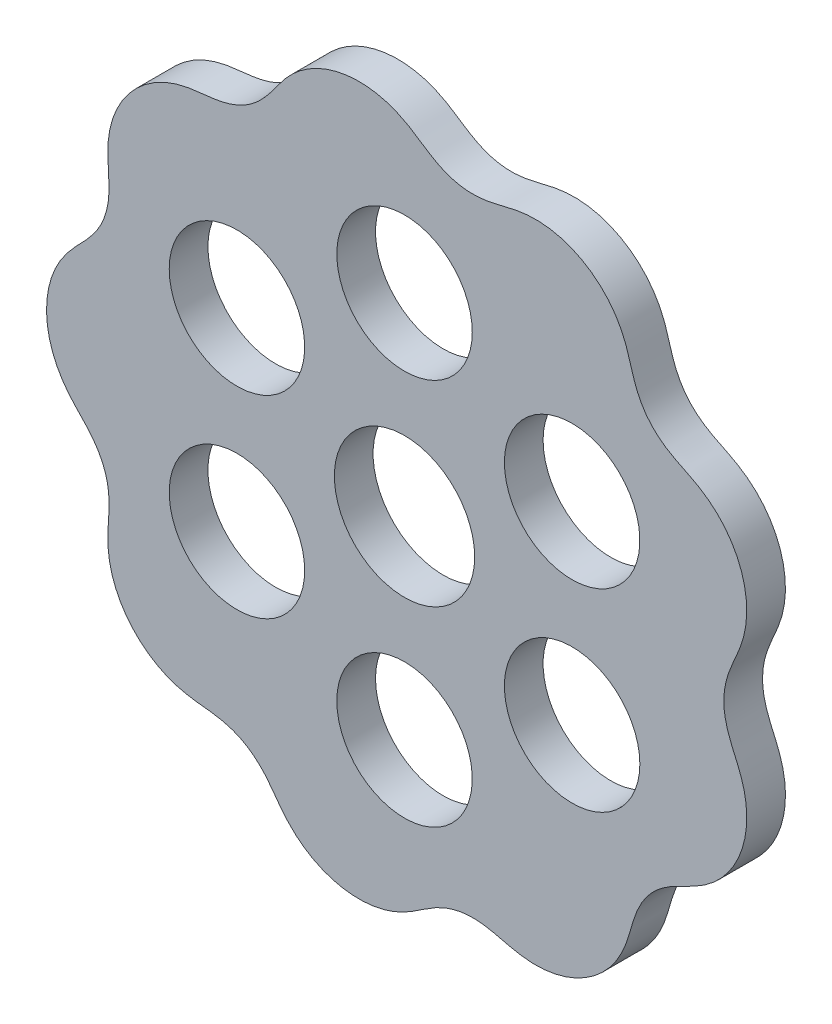
SolidWorks part; units mm, degrees
ref_plane "Front Plane" through (0, 0, 0) normal (0, 0, 1) x (1, 0, 0)
ref_plane "Top Plane" through (0, 0, 0) normal (0, 1, 0) x (1, 0, 0)
ref_plane "Right Plane" through (0, 0, 0) normal (1, 0, 0) x (0, 0, -1)
curve "Curve2"
  spline degree 3 poles (33.0063, -0.3751, 0) (32.9968, 0, 0) (33.0063, 0.3751, 0) (33.034, 0.7448, 0) (33.0785, 1.1045, 0) (33.1373, 1.45, 0) (33.2077, 1.7787, 0) (33.2869, 2.0891, 0) (33.3721, 2.3805, 0) (33.4609, 2.6535, 0) (33.5515, 2.909, 0) (33.6424, 3.1486, 0) (33.7324, 3.3741, 0) (33.821, 3.5871, 0) (33.9077, 3.7897, 0) (33.9923, 3.9834, 0) (34.0747, 4.17, 0) (34.1549, 4.3509, 0) (34.2329, 4.5275, 0) (34.3089, 4.701, 0) (34.383, 4.8725, 0) (34.4551, 5.0429, 0) (34.5253, 5.2131, 0) (34.5937, 5.3838, 0) (34.6602, 5.5556, 0) (34.7247, 5.7292, 0) (34.7873, 5.9049, 0) (34.8477, 6.0832, 0) (34.9059, 6.2645, 0) (34.9616, 6.4489, 0) (35.0148, 6.6368, 0) (35.0651, 6.8282, 0) (35.1125, 7.0234, 0) (35.1566, 7.2223, 0) (35.1972, 7.4251, 0) (35.2342, 7.6317, 0) (35.2672, 7.8421, 0) (35.2961, 8.0561, 0) (35.3206, 8.2737, 0) (35.3404, 8.4948, 0) (35.3554, 8.7191, 0) (35.3653, 8.9466, 0) (35.3699, 9.1768, 0) (35.3692, 9.4097, 0) (35.3628, 9.6449, 0) (35.3506, 9.8822, 0) (35.3325, 10.1213, 0) (35.3084, 10.3618, 0) (35.2782, 10.6035, 0) (35.2418, 10.846, 0) (35.1992, 11.0889, 0) (35.1503, 11.332, 0) (35.0951, 11.5748, 0) (35.0336, 11.817, 0) (34.9658, 12.0583, 0) (34.8919, 12.2983, 0) (34.8119, 12.5367, 0) (34.7259, 12.773, 0) (34.634, 13.007, 0) (34.5363, 13.2384, 0) (34.4331, 13.4668, 0) (34.3245, 13.6919, 0) (34.2107, 13.9134, 0) (34.0919, 14.131, 0) (33.9685, 14.3445, 0) (33.8405, 14.5537, 0) (33.7083, 14.7582, 0) (33.5721, 14.958, 0) (33.4323, 15.1527, 0) (33.2891, 15.3423, 0) (33.1428, 15.5266, 0) (32.9937, 15.7055, 0) (32.8421, 15.8789, 0) (32.6883, 16.0467, 0) (32.5327, 16.209, 0) (32.3754, 16.3656, 0) (32.2168, 16.5165, 0) (32.0571, 16.662, 0) (31.8965, 16.8019, 0) (31.7354, 16.9364, 0) (31.5739, 17.0656, 0) (31.4123, 17.1896, 0) (31.2505, 17.3087, 0) (31.0889, 17.423, 0) (30.9274, 17.5327, 0) (30.7662, 17.6382, 0) (30.6051, 17.7396, 0) (30.4442, 17.8374, 0) (30.2833, 17.9318, 0) (30.1223, 18.0233, 0) (29.9609, 18.1122, 0) (29.7988, 18.199, 0) (29.6356, 18.2842, 0) (29.4709, 18.3684, 0) (29.3039, 18.4522, 0) (29.1342, 18.5362, 0) (28.9609, 18.6213, 0) (28.7832, 18.7084, 0) (28.6001, 18.7984, 0) (28.4108, 18.8924, 0) (28.2142, 18.9918, 0) (28.0094, 19.0981, 0) (27.7954, 19.2129, 0) (27.5718, 19.3381, 0) (27.3382, 19.4756, 0) (27.0947, 19.6276, 0) (26.8421, 19.7961, 0) (26.582, 19.9829, 0) (26.3167, 20.1895, 0) (26.0495, 20.4164, 0) (25.7843, 20.6633, 0) (25.5254, 20.9287, 0) (25.2771, 21.21, 0) (25.0432, 21.5034, 0) (24.8267, 21.8044, 0) (24.6296, 22.1085, 0) (24.4526, 22.411, 0) (24.2953, 22.7081, 0) (24.1564, 22.9967, 0) (24.0344, 23.2747, 0) (23.927, 23.541, 0) (23.8321, 23.7949, 0) (23.7476, 24.0369, 0) (23.6717, 24.2675, 0) (23.6026, 24.4877, 0) (23.5389, 24.6985, 0) (23.4791, 24.9013, 0) (23.4223, 25.0972, 0) (23.3674, 25.2873, 0) (23.3137, 25.4728, 0) (23.2604, 25.6546, 0) (23.2069, 25.8335, 0) (23.1526, 26.0104, 0) (23.097, 26.1859, 0) (23.0397, 26.3606, 0) (22.9801, 26.535, 0) (22.918, 26.7094, 0) (22.853, 26.8842, 0) (22.7847, 27.0597, 0) (22.7127, 27.2359, 0) (22.6369, 27.413, 0) (22.5568, 27.5911, 0) (22.4723, 27.7701, 0) (22.3832, 27.9501, 0) (22.2891, 28.1309, 0) (22.1899, 28.3123, 0) (22.0854, 28.4943, 0) (21.9755, 28.6767, 0) (21.86, 28.8592, 0) (21.7389, 29.0417, 0) (21.6119, 29.2238, 0) (21.4792, 29.4052, 0) (21.3406, 29.5858, 0) (21.1962, 29.7652, 0) (21.0459, 29.9431, 0) (20.8898, 30.1192, 0) (20.728, 30.2931, 0) (20.5605, 30.4647, 0) (20.3874, 30.6334, 0) (20.2089, 30.7991, 0) (20.0252, 30.9615, 0) (19.8363, 31.1202, 0) (19.6426, 31.2749, 0) (19.4442, 31.4255, 0) (19.2414, 31.5715, 0) (19.0344, 31.7128, 0) (18.8236, 31.8491, 0) (18.609, 31.9803, 0) (18.3912, 32.1061, 0) (18.1704, 32.2262, 0) (17.9469, 32.3407, 0) (17.721, 32.4493, 0) (17.4931, 32.5519, 0) (17.2636, 32.6485, 0) (17.0327, 32.7389, 0) (16.8009, 32.823, 0) (16.5684, 32.901, 0) (16.3356, 32.9727, 0) (16.1029, 33.0382, 0) (15.8706, 33.0975, 0) (15.6391, 33.1507, 0) (15.4085, 33.1978, 0) (15.1793, 33.2391, 0) (14.9518, 33.2745, 0) (14.7261, 33.3042, 0) (14.5026, 33.3284, 0) (14.2814, 33.3472, 0) (14.0628, 33.3609, 0) (13.847, 33.3697, 0) (13.6341, 33.3737, 0) (13.4243, 33.3732, 0) (13.2175, 33.3683, 0) (13.0139, 33.3594, 0) (12.8135, 33.3467, 0) (12.6162, 33.3303, 0) (12.4219, 33.3106, 0) (12.2306, 33.2877, 0) (12.042, 33.2619, 0) (11.8559, 33.2334, 0) (11.672, 33.2023, 0) (11.4899, 33.1689, 0) (11.3091, 33.1332, 0) (11.1291, 33.0955, 0) (10.9493, 33.0559, 0) (10.769, 33.0145, 0) (10.5873, 32.9714, 0) (10.4032, 32.9267, 0) (10.2158, 32.8805, 0) (10.0237, 32.8329, 0) (9.8256, 32.7842, 0) (9.6201, 32.7345, 0) (9.4056, 32.6843, 0) (9.1804, 32.6341, 0) (8.9427, 32.5845, 0) (8.691, 32.5366, 0) (8.4236, 32.4918, 0) (8.1393, 32.4517, 0) (7.8375, 32.4185, 0) (7.5182, 32.3944, 0) (7.1822, 32.3821, 0) (6.8317, 32.3841, 0) (6.4698, 32.4028, 0) (6.1009, 32.4397, 0) (5.7298, 32.4956, 0) (5.3621, 32.57, 0) (5.0028, 32.6615, 0) (4.6563, 32.7677, 0) (4.3262, 32.8857, 0) (4.0147, 33.0121, 0) (3.7229, 33.144, 0) (3.4507, 33.2785, 0) (3.1973, 33.4134, 0) (2.9613, 33.5469, 0) (2.7411, 33.678, 0) (2.5348, 33.8059, 0) (2.3403, 33.9301, 0) (2.1559, 34.0507, 0) (1.9798, 34.1676, 0) (1.8104, 34.2812, 0) (1.6461, 34.3915, 0) (1.4857, 34.4991, 0) (1.3281, 34.604, 0) (1.1721, 34.7067, 0) (1.0168, 34.8073, 0) (0.8614, 34.906, 0) (0.7051, 35.003, 0) (0.5475, 35.0983, 0) (0.3878, 35.192, 0) (0.2256, 35.2841, 0) (0.0604, 35.3746, 0) (-0.1079, 35.4634, 0) (-0.2799, 35.5503, 0) (-0.4557, 35.6353, 0) (-0.6355, 35.7181, 0) (-0.8195, 35.7986, 0) (-1.0077, 35.8766, 0) (-1.2004, 35.9519, 0) (-1.3974, 36.0242, 0) (-1.5988, 36.0932, 0) (-1.8046, 36.1588, 0) (-2.0147, 36.2207, 0) (-2.229, 36.2786, 0) (-2.4473, 36.3323, 0) (-2.6695, 36.3816, 0) (-2.8955, 36.4261, 0) (-3.125, 36.4658, 0) (-3.3577, 36.5003, 0) (-3.5935, 36.5296, 0) (-3.8321, 36.5533, 0) (-4.0731, 36.5713, 0) (-4.3164, 36.5835, 0) (-4.5615, 36.5898, 0) (-4.8082, 36.59, 0) (-5.056, 36.584, 0) (-5.3047, 36.5718, 0) (-5.554, 36.5533, 0) (-5.8034, 36.5285, 0) (-6.0526, 36.4974, 0) (-6.3012, 36.46, 0) (-6.5489, 36.4163, 0) (-6.7953, 36.3664, 0) (-7.0401, 36.3104, 0) (-7.2829, 36.2485, 0) (-7.5235, 36.1806, 0) (-7.7614, 36.107, 0) (-7.9963, 36.0278, 0) (-8.228, 35.9433, 0) (-8.4562, 35.8536, 0) (-8.6806, 35.7589, 0) (-8.901, 35.6595, 0) (-9.1171, 35.5556, 0) (-9.3286, 35.4475, 0) (-9.5355, 35.3354, 0) (-9.7376, 35.2197, 0) (-9.9347, 35.1005, 0) (-10.1267, 34.9782, 0) (-10.3135, 34.8531, 0) (-10.495, 34.7254, 0) (-10.6712, 34.5954, 0) (-10.8422, 34.4634, 0) (-11.0078, 34.3296, 0) (-11.1683, 34.1943, 0) (-11.3236, 34.0577, 0) (-11.4738, 33.92, 0) (-11.6191, 33.7814, 0) (-11.7598, 33.6421, 0) (-11.8959, 33.5021, 0) (-12.0277, 33.3616, 0) (-12.1556, 33.2206, 0) (-12.2798, 33.0791, 0) (-12.4007, 32.9371, 0) (-12.5188, 32.7944, 0) (-12.6343, 32.6509, 0) (-12.748, 32.5063, 0) (-12.8602, 32.3604, 0) (-12.9718, 32.2128, 0) (-13.0833, 32.0629, 0) (-13.1955, 31.9104, 0) (-13.3094, 31.7545, 0) (-13.426, 31.5946, 0) (-13.5464, 31.4299, 0) (-13.6719, 31.2598, 0) (-13.804, 31.0834, 0) (-13.9442, 30.9002, 0) (-14.0944, 30.7095, 0) (-14.2565, 30.511, 0) (-14.4325, 30.3048, 0) (-14.6245, 30.0913, 0) (-14.8343, 29.8718, 0) (-15.0634, 29.6481, 0) (-15.3129, 29.4227, 0) (-15.5827, 29.199, 0) (-15.8719, 28.9807, 0) (-16.1783, 28.7718, 0) (-16.4984, 28.5761, 0) (-16.828, 28.3967, 0) (-17.1621, 28.2359, 0) (-17.4957, 28.0945, 0) (-17.8244, 27.9727, 0) (-18.1443, 27.8694, 0) (-18.4526, 27.7828, 0) (-18.7476, 27.7108, 0) (-19.0284, 27.6513, 0) (-19.295, 27.602, 0) (-19.548, 27.5608, 0) (-19.7882, 27.5261, 0) (-20.0171, 27.4963, 0) (-20.2358, 27.4701, 0) (-20.4459, 27.4465, 0) (-20.6487, 27.4245, 0) (-20.8455, 27.4035, 0) (-21.0374, 27.3828, 0) (-21.2257, 27.3619, 0) (-21.4112, 27.3403, 0) (-21.5948, 27.3175, 0) (-21.7773, 27.2932, 0) (-21.9593, 27.2671, 0) (-22.1414, 27.2388, 0) (-22.324, 27.2079, 0) (-22.5074, 27.1742, 0) (-22.6921, 27.1374, 0) (-22.8781, 27.0971, 0) (-23.0657, 27.0532, 0) (-23.255, 27.0053, 0) (-23.446, 26.9532, 0) (-23.6387, 26.8966, 0) (-23.833, 26.8353, 0) (-24.029, 26.7691, 0) (-24.2264, 26.6979, 0) (-24.4251, 26.6213, 0) (-24.6249, 26.5393, 0) (-24.8256, 26.4516, 0) (-25.0269, 26.3583, 0) (-25.2287, 26.2591, 0) (-25.4306, 26.154, 0) (-25.6323, 26.0429, 0) (-25.8336, 25.9257, 0) (-26.0341, 25.8026, 0) (-26.2335, 25.6734, 0) (-26.4315, 25.5382, 0) (-26.6278, 25.3971, 0) (-26.822, 25.2501, 0) (-27.0138, 25.0973, 0) (-27.2029, 24.9389, 0) (-27.3889, 24.775, 0) (-27.5716, 24.6058, 0) (-27.7506, 24.4314, 0) (-27.9257, 24.2521, 0) (-28.0966, 24.0681, 0) (-28.263, 23.8797, 0) (-28.4247, 23.687, 0) (-28.5814, 23.4904, 0) (-28.7329, 23.2901, 0) (-28.8791, 23.0866, 0) (-29.0198, 22.88, 0) (-29.1547, 22.6707, 0) (-29.2838, 22.459, 0) (-29.4069, 22.2453, 0) (-29.5241, 22.0299, 0) (-29.6351, 21.8131, 0) (-29.74, 21.5953, 0) (-29.8388, 21.3769, 0) (-29.9314, 21.158, 0) (-30.0178, 20.9392, 0) (-30.0982, 20.7206, 0) (-30.1726, 20.5027, 0) (-30.2411, 20.2856, 0) (-30.3037, 20.0696, 0) (-30.3607, 19.8551, 0) (-30.4121, 19.6423, 0) (-30.4582, 19.4312, 0) (-30.4991, 19.2223, 0) (-30.5351, 19.0155, 0) (-30.5662, 18.8111, 0) (-30.5928, 18.609, 0) (-30.615, 18.4094, 0) (-30.6332, 18.2123, 0) (-30.6475, 18.0176, 0) (-30.6582, 17.8252, 0) (-30.6655, 17.635, 0) (-30.6697, 17.4467, 0) (-30.6711, 17.2602, 0) (-30.6698, 17.075, 0) (-30.666, 16.8908, 0) (-30.6602, 16.707, 0) (-30.6524, 16.5231, 0) (-30.6429, 16.3383, 0) (-30.632, 16.1519, 0) (-30.6199, 15.9628, 0) (-30.607, 15.7702, 0) (-30.5935, 15.5728, 0) (-30.5799, 15.3693, 0) (-30.5667, 15.1583, 0) (-30.5545, 14.9383, 0) (-30.5441, 14.7078, 0) (-30.5366, 14.4651, 0) (-30.5332, 14.2089, 0) (-30.5355, 13.9378, 0) (-30.5453, 13.6509, 0) (-30.565, 13.3479, 0) (-30.5967, 13.0292, 0) (-30.6429, 12.6962, 0) (-30.7058, 12.3513, 0) (-30.7871, 11.9982, 0) (-30.8875, 11.6413, 0) (-31.0069, 11.2856, 0) (-31.144, 10.9363, 0) (-31.2966, 10.5984, 0) (-31.4613, 10.2756, 0) (-31.6348, 9.9711, 0) (-31.8134, 9.6863, 0) (-31.994, 9.4217, 0) (-32.1737, 9.177, 0) (-32.3505, 8.9509, 0) (-32.5231, 8.7417, 0) (-32.6904, 8.5476, 0) (-32.8521, 8.3666, 0) (-33.0082, 8.1967, 0) (-33.159, 8.036, 0) (-33.3047, 7.8829, 0) (-33.446, 7.7357, 0) (-33.5832, 7.5931, 0) (-33.7169, 7.4539, 0) (-33.8477, 7.3168, 0) (-33.9759, 7.181, 0) (-34.1019, 7.0455, 0) (-34.2261, 6.9096, 0) (-34.3488, 6.7726, 0) (-34.47, 6.6339, 0) (-34.59, 6.4929, 0) (-34.7089, 6.3492, 0) (-34.8267, 6.2023, 0) (-34.9433, 6.0518, 0) (-35.0588, 5.8976, 0) (-35.173, 5.7392, 0) (-35.2858, 5.5765, 0) (-35.3971, 5.4093, 0) (-35.5066, 5.2375, 0) (-35.6141, 5.0608, 0) (-35.7195, 4.8794, 0) (-35.8225, 4.693, 0) (-35.9228, 4.5017, 0) (-36.0203, 4.3056, 0) (-36.1145, 4.1046, 0) (-36.2053, 3.8989, 0) (-36.2924, 3.6886, 0) (-36.3755, 3.4738, 0) (-36.4544, 3.2547, 0) (-36.5289, 3.0315, 0) (-36.5986, 2.8044, 0) (-36.6634, 2.5735, 0) (-36.723, 2.3393, 0) (-36.7773, 2.1019, 0) (-36.826, 1.8615, 0) (-36.869, 1.6187, 0) (-36.9062, 1.3735, 0) (-36.9374, 1.1265, 0) (-36.9624, 0.8778, 0) (-36.9813, 0.6279, 0) (-36.9939, 0.3771, 0) (-37.0003, 0.1258, 0) (-37.0003, -0.1258, 0) (-36.9939, -0.3771, 0) (-36.9813, -0.6279, 0) (-36.9624, -0.8778, 0) (-36.9374, -1.1265, 0) (-36.9062, -1.3735, 0) (-36.869, -1.6187, 0) (-36.826, -1.8615, 0) (-36.7773, -2.1019, 0) (-36.723, -2.3393, 0) (-36.6634, -2.5735, 0) (-36.5986, -2.8044, 0) (-36.5289, -3.0315, 0) (-36.4544, -3.2547, 0) (-36.3755, -3.4738, 0) (-36.2924, -3.6886, 0) (-36.2053, -3.8989, 0) (-36.1145, -4.1046, 0) (-36.0203, -4.3056, 0) (-35.9228, -4.5017, 0) (-35.8225, -4.693, 0) (-35.7195, -4.8794, 0) (-35.6141, -5.0608, 0) (-35.5066, -5.2375, 0) (-35.3971, -5.4093, 0) (-35.2858, -5.5765, 0) (-35.173, -5.7392, 0) (-35.0588, -5.8976, 0) (-34.9433, -6.0518, 0) (-34.8267, -6.2023, 0) (-34.7089, -6.3492, 0) (-34.59, -6.4929, 0) (-34.47, -6.6339, 0) (-34.3488, -6.7726, 0) (-34.2261, -6.9096, 0) (-34.1019, -7.0455, 0) (-33.9759, -7.181, 0) (-33.8477, -7.3168, 0) (-33.7169, -7.4539, 0) (-33.5832, -7.5931, 0) (-33.446, -7.7357, 0) (-33.3047, -7.8829, 0) (-33.159, -8.036, 0) (-33.0082, -8.1967, 0) (-32.8521, -8.3666, 0) (-32.6904, -8.5476, 0) (-32.5231, -8.7417, 0) (-32.3505, -8.9509, 0) (-32.1737, -9.177, 0) (-31.994, -9.4217, 0) (-31.8134, -9.6863, 0) (-31.6348, -9.9711, 0) (-31.4613, -10.2756, 0) (-31.2966, -10.5984, 0) (-31.144, -10.9363, 0) (-31.0069, -11.2856, 0) (-30.8875, -11.6413, 0) (-30.7871, -11.9982, 0) (-30.7058, -12.3513, 0) (-30.6429, -12.6962, 0) (-30.5967, -13.0292, 0) (-30.565, -13.3479, 0) (-30.5453, -13.6509, 0) (-30.5355, -13.9378, 0) (-30.5332, -14.2089, 0) (-30.5366, -14.4651, 0) (-30.5441, -14.7078, 0) (-30.5545, -14.9383, 0) (-30.5667, -15.1583, 0) (-30.5799, -15.3693, 0) (-30.5935, -15.5728, 0) (-30.607, -15.7702, 0) (-30.6199, -15.9628, 0) (-30.632, -16.1519, 0) (-30.6429, -16.3383, 0) (-30.6524, -16.5231, 0) (-30.6602, -16.707, 0) (-30.666, -16.8908, 0) (-30.6698, -17.075, 0) (-30.6711, -17.2602, 0) (-30.6697, -17.4467, 0) (-30.6655, -17.635, 0) (-30.6582, -17.8252, 0) (-30.6475, -18.0176, 0) (-30.6332, -18.2123, 0) (-30.615, -18.4094, 0) (-30.5928, -18.609, 0) (-30.5662, -18.8111, 0) (-30.5351, -19.0155, 0) (-30.4991, -19.2223, 0) (-30.4582, -19.4312, 0) (-30.4121, -19.6423, 0) (-30.3607, -19.8551, 0) (-30.3037, -20.0696, 0) (-30.2411, -20.2856, 0) (-30.1726, -20.5027, 0) (-30.0982, -20.7206, 0) (-30.0178, -20.9392, 0) (-29.9314, -21.158, 0) (-29.8388, -21.3769, 0) (-29.74, -21.5953, 0) (-29.6351, -21.8131, 0) (-29.5241, -22.0299, 0) (-29.4069, -22.2453, 0) (-29.2838, -22.459, 0) (-29.1547, -22.6707, 0) (-29.0198, -22.88, 0) (-28.8791, -23.0866, 0) (-28.7329, -23.2901, 0) (-28.5814, -23.4904, 0) (-28.4247, -23.687, 0) (-28.263, -23.8797, 0) (-28.0966, -24.0681, 0) (-27.9257, -24.2521, 0) (-27.7506, -24.4314, 0) (-27.5716, -24.6058, 0) (-27.3889, -24.775, 0) (-27.2029, -24.9389, 0) (-27.0138, -25.0973, 0) (-26.822, -25.2501, 0) (-26.6278, -25.3971, 0) (-26.4315, -25.5382, 0) (-26.2335, -25.6734, 0) (-26.0341, -25.8026, 0) (-25.8336, -25.9257, 0) (-25.6323, -26.0429, 0) (-25.4306, -26.154, 0) (-25.2287, -26.2591, 0) (-25.0269, -26.3583, 0) (-24.8256, -26.4516, 0) (-24.6249, -26.5393, 0) (-24.4251, -26.6213, 0) (-24.2264, -26.6979, 0) (-24.029, -26.7691, 0) (-23.833, -26.8353, 0) (-23.6387, -26.8966, 0) (-23.446, -26.9532, 0) (-23.255, -27.0053, 0) (-23.0657, -27.0532, 0) (-22.8781, -27.0971, 0) (-22.6921, -27.1374, 0) (-22.5074, -27.1742, 0) (-22.324, -27.2079, 0) (-22.1414, -27.2388, 0) (-21.9593, -27.2671, 0) (-21.7773, -27.2932, 0) (-21.5948, -27.3175, 0) (-21.4112, -27.3403, 0) (-21.2257, -27.3619, 0) (-21.0374, -27.3828, 0) (-20.8455, -27.4035, 0) (-20.6487, -27.4245, 0) (-20.4459, -27.4465, 0) (-20.2358, -27.4701, 0) (-20.0171, -27.4963, 0) (-19.7882, -27.5261, 0) (-19.548, -27.5608, 0) (-19.295, -27.602, 0) (-19.0284, -27.6513, 0) (-18.7476, -27.7108, 0) (-18.4526, -27.7828, 0) (-18.1443, -27.8694, 0) (-17.8244, -27.9727, 0) (-17.4957, -28.0945, 0) (-17.1621, -28.2359, 0) (-16.828, -28.3967, 0) (-16.4984, -28.5761, 0) (-16.1783, -28.7718, 0) (-15.8719, -28.9807, 0) (-15.5827, -29.199, 0) (-15.3129, -29.4227, 0) (-15.0634, -29.6481, 0) (-14.8343, -29.8718, 0) (-14.6245, -30.0913, 0) (-14.4325, -30.3048, 0) (-14.2565, -30.511, 0) (-14.0944, -30.7095, 0) (-13.9442, -30.9002, 0) (-13.804, -31.0834, 0) (-13.6719, -31.2598, 0) (-13.5464, -31.4299, 0) (-13.426, -31.5946, 0) (-13.3094, -31.7545, 0) (-13.1955, -31.9104, 0) (-13.0833, -32.0629, 0) (-12.9718, -32.2128, 0) (-12.8602, -32.3604, 0) (-12.748, -32.5063, 0) (-12.6343, -32.6509, 0) (-12.5188, -32.7944, 0) (-12.4007, -32.9371, 0) (-12.2798, -33.0791, 0) (-12.1556, -33.2206, 0) (-12.0277, -33.3616, 0) (-11.8959, -33.5021, 0) (-11.7598, -33.6421, 0) (-11.6191, -33.7814, 0) (-11.4738, -33.92, 0) (-11.3236, -34.0577, 0) (-11.1683, -34.1943, 0) (-11.0078, -34.3296, 0) (-10.8422, -34.4634, 0) (-10.6712, -34.5954, 0) (-10.495, -34.7254, 0) (-10.3135, -34.8531, 0) (-10.1267, -34.9782, 0) (-9.9347, -35.1005, 0) (-9.7376, -35.2197, 0) (-9.5355, -35.3354, 0) (-9.3286, -35.4475, 0) (-9.1171, -35.5556, 0) (-8.901, -35.6595, 0) (-8.6806, -35.7589, 0) (-8.4562, -35.8536, 0) (-8.228, -35.9433, 0) (-7.9963, -36.0278, 0) (-7.7614, -36.107, 0) (-7.5235, -36.1806, 0) (-7.2829, -36.2485, 0) (-7.0401, -36.3104, 0) (-6.7953, -36.3664, 0) (-6.5489, -36.4163, 0) (-6.3012, -36.46, 0) (-6.0526, -36.4974, 0) (-5.8034, -36.5285, 0) (-5.554, -36.5533, 0) (-5.3047, -36.5718, 0) (-5.056, -36.584, 0) (-4.8082, -36.59, 0) (-4.5615, -36.5898, 0) (-4.3164, -36.5835, 0) (-4.0731, -36.5713, 0) (-3.8321, -36.5533, 0) (-3.5935, -36.5296, 0) (-3.3577, -36.5003, 0) (-3.125, -36.4658, 0) (-2.8955, -36.4261, 0) (-2.6695, -36.3816, 0) (-2.4473, -36.3323, 0) (-2.229, -36.2786, 0) (-2.0147, -36.2207, 0) (-1.8046, -36.1588, 0) (-1.5988, -36.0932, 0) (-1.3974, -36.0242, 0) (-1.2004, -35.9519, 0) (-1.0077, -35.8766, 0) (-0.8195, -35.7986, 0) (-0.6355, -35.7181, 0) (-0.4557, -35.6353, 0) (-0.2799, -35.5503, 0) (-0.1079, -35.4634, 0) (0.0604, -35.3746, 0) (0.2256, -35.2841, 0) (0.3878, -35.192, 0) (0.5475, -35.0983, 0) (0.7051, -35.003, 0) (0.8614, -34.906, 0) (1.0168, -34.8073, 0) (1.1721, -34.7067, 0) (1.3281, -34.604, 0) (1.4857, -34.4991, 0) (1.6461, -34.3915, 0) (1.8104, -34.2812, 0) (1.9798, -34.1676, 0) (2.1559, -34.0507, 0) (2.3403, -33.9301, 0) (2.5348, -33.8059, 0) (2.7411, -33.678, 0) (2.9613, -33.5469, 0) (3.1973, -33.4134, 0) (3.4507, -33.2785, 0) (3.7229, -33.144, 0) (4.0147, -33.0121, 0) (4.3262, -32.8857, 0) (4.6563, -32.7677, 0) (5.0028, -32.6615, 0) (5.3621, -32.57, 0) (5.7298, -32.4956, 0) (6.1009, -32.4397, 0) (6.4698, -32.4028, 0) (6.8317, -32.3841, 0) (7.1822, -32.3821, 0) (7.5182, -32.3944, 0) (7.8375, -32.4185, 0) (8.1393, -32.4517, 0) (8.4236, -32.4918, 0) (8.691, -32.5366, 0) (8.9427, -32.5845, 0) (9.1804, -32.6341, 0) (9.4056, -32.6843, 0) (9.6201, -32.7345, 0) (9.8256, -32.7842, 0) (10.0237, -32.8329, 0) (10.2158, -32.8805, 0) (10.4032, -32.9267, 0) (10.5873, -32.9714, 0) (10.769, -33.0145, 0) (10.9493, -33.0559, 0) (11.1291, -33.0955, 0) (11.3091, -33.1332, 0) (11.4899, -33.1689, 0) (11.672, -33.2023, 0) (11.8559, -33.2334, 0) (12.042, -33.2619, 0) (12.2306, -33.2877, 0) (12.4219, -33.3106, 0) (12.6162, -33.3303, 0) (12.8135, -33.3467, 0) (13.0139, -33.3594, 0) (13.2175, -33.3683, 0) (13.4243, -33.3732, 0) (13.6341, -33.3737, 0) (13.847, -33.3697, 0) (14.0628, -33.3609, 0) (14.2814, -33.3472, 0) (14.5026, -33.3284, 0) (14.7261, -33.3042, 0) (14.9518, -33.2745, 0) (15.1793, -33.2391, 0) (15.4085, -33.1978, 0) (15.6391, -33.1507, 0) (15.8706, -33.0975, 0) (16.1029, -33.0382, 0) (16.3356, -32.9727, 0) (16.5684, -32.901, 0) (16.8009, -32.823, 0) (17.0327, -32.7389, 0) (17.2636, -32.6485, 0) (17.4931, -32.5519, 0) (17.721, -32.4493, 0) (17.9469, -32.3407, 0) (18.1704, -32.2262, 0) (18.3912, -32.1061, 0) (18.609, -31.9803, 0) (18.8236, -31.8491, 0) (19.0344, -31.7128, 0) (19.2414, -31.5715, 0) (19.4442, -31.4255, 0) (19.6426, -31.2749, 0) (19.8363, -31.1202, 0) (20.0252, -30.9615, 0) (20.2089, -30.7991, 0) (20.3874, -30.6334, 0) (20.5605, -30.4647, 0) (20.728, -30.2931, 0) (20.8898, -30.1192, 0) (21.0459, -29.9431, 0) (21.1962, -29.7652, 0) (21.3406, -29.5858, 0) (21.4792, -29.4052, 0) (21.6119, -29.2238, 0) (21.7389, -29.0417, 0) (21.86, -28.8592, 0) (21.9755, -28.6767, 0) (22.0854, -28.4943, 0) (22.1899, -28.3123, 0) (22.2891, -28.1309, 0) (22.3832, -27.9501, 0) (22.4723, -27.7701, 0) (22.5568, -27.5911, 0) (22.6369, -27.413, 0) (22.7127, -27.2359, 0) (22.7847, -27.0597, 0) (22.853, -26.8842, 0) (22.918, -26.7094, 0) (22.9801, -26.535, 0) (23.0397, -26.3606, 0) (23.097, -26.1859, 0) (23.1526, -26.0104, 0) (23.2069, -25.8335, 0) (23.2604, -25.6546, 0) (23.3137, -25.4728, 0) (23.3674, -25.2873, 0) (23.4223, -25.0972, 0) (23.4791, -24.9013, 0) (23.5389, -24.6985, 0) (23.6026, -24.4877, 0) (23.6717, -24.2675, 0) (23.7476, -24.0369, 0) (23.8321, -23.7949, 0) (23.927, -23.541, 0) (24.0344, -23.2747, 0) (24.1564, -22.9967, 0) (24.2953, -22.7081, 0) (24.4526, -22.411, 0) (24.6296, -22.1085, 0) (24.8267, -21.8044, 0) (25.0432, -21.5034, 0) (25.2771, -21.21, 0) (25.5254, -20.9287, 0) (25.7843, -20.6633, 0) (26.0495, -20.4164, 0) (26.3167, -20.1895, 0) (26.582, -19.9829, 0) (26.8421, -19.7961, 0) (27.0947, -19.6276, 0) (27.3382, -19.4756, 0) (27.5718, -19.3381, 0) (27.7954, -19.2129, 0) (28.0094, -19.0981, 0) (28.2142, -18.9918, 0) (28.4108, -18.8924, 0) (28.6001, -18.7984, 0) (28.7832, -18.7084, 0) (28.9609, -18.6213, 0) (29.1342, -18.5362, 0) (29.3039, -18.4522, 0) (29.4709, -18.3684, 0) (29.6356, -18.2842, 0) (29.7988, -18.199, 0) (29.9609, -18.1122, 0) (30.1223, -18.0233, 0) (30.2833, -17.9318, 0) (30.4442, -17.8374, 0) (30.6051, -17.7396, 0) (30.7662, -17.6382, 0) (30.9274, -17.5327, 0) (31.0889, -17.423, 0) (31.2505, -17.3087, 0) (31.4123, -17.1896, 0) (31.5739, -17.0656, 0) (31.7354, -16.9364, 0) (31.8965, -16.8019, 0) (32.0571, -16.662, 0) (32.2168, -16.5165, 0) (32.3754, -16.3656, 0) (32.5327, -16.209, 0) (32.6883, -16.0467, 0) (32.8421, -15.8789, 0) (32.9937, -15.7055, 0) (33.1428, -15.5266, 0) (33.2891, -15.3423, 0) (33.4323, -15.1527, 0) (33.5721, -14.958, 0) (33.7083, -14.7582, 0) (33.8405, -14.5537, 0) (33.9685, -14.3445, 0) (34.0919, -14.131, 0) (34.2107, -13.9134, 0) (34.3245, -13.6919, 0) (34.4331, -13.4668, 0) (34.5363, -13.2384, 0) (34.634, -13.007, 0) (34.7259, -12.773, 0) (34.8119, -12.5367, 0) (34.8919, -12.2983, 0) (34.9658, -12.0583, 0) (35.0336, -11.817, 0) (35.0951, -11.5748, 0) (35.1503, -11.332, 0) (35.1992, -11.0889, 0) (35.2418, -10.846, 0) (35.2782, -10.6035, 0) (35.3084, -10.3618, 0) (35.3325, -10.1213, 0) (35.3506, -9.8822, 0) (35.3628, -9.6449, 0) (35.3692, -9.4097, 0) (35.3699, -9.1768, 0) (35.3653, -8.9466, 0) (35.3554, -8.7191, 0) (35.3404, -8.4948, 0) (35.3206, -8.2737, 0) (35.2961, -8.0561, 0) (35.2672, -7.8421, 0) (35.2342, -7.6317, 0) (35.1972, -7.4251, 0) (35.1566, -7.2223, 0) (35.1125, -7.0234, 0) (35.0651, -6.8282, 0) (35.0148, -6.6368, 0) (34.9616, -6.4489, 0) (34.9059, -6.2645, 0) (34.8477, -6.0832, 0) (34.7873, -5.9049, 0) (34.7247, -5.7292, 0) (34.6602, -5.5556, 0) (34.5937, -5.3838, 0) (34.5253, -5.2131, 0) (34.4551, -5.0429, 0) (34.383, -4.8725, 0) (34.3089, -4.701, 0) (34.2329, -4.5275, 0) (34.1549, -4.3509, 0) (34.0747, -4.17, 0) (33.9923, -3.9834, 0) (33.9077, -3.7897, 0) (33.821, -3.5871, 0) (33.7324, -3.3741, 0) (33.6424, -3.1486, 0) (33.5515, -2.909, 0) (33.4609, -2.6535, 0) (33.3721, -2.3805, 0) (33.2869, -2.0891, 0) (33.2077, -1.7787, 0) (33.1373, -1.45, 0) (33.0785, -1.1045, 0) (33.034, -0.7448, 0) (33.0063, -0.3751, 0) (32.9968, 0, 0) (33.0063, 0.3751, 0) knots -0.004714 -0.003174 -0.001596 0 0.001596 0.003174 0.004714 0.006203 0.00763 0.008989 0.010276 0.011492 0.012639 0.013724 0.014751 0.015727 0.016659 0.017553 0.018415 0.019253 0.02007 0.020871 0.021662 0.022445 0.023225 0.024003 0.024784 0.025568 0.026358 0.027156 0.027963 0.028779 0.029606 0.030446 0.031297 0.032161 0.033037 0.033927 0.03483 0.035745 0.036674 0.037615 0.038568 0.039533 0.04051 0.041497 0.042495 0.043502 0.044519 0.045544 0.046576 0.047616 0.048662 0.049713 0.050769 0.051829 0.052891 0.053956 0.055022 0.056089 0.057155 0.05822 0.059282 0.060342 0.061398 0.062449 0.063495 0.064535 0.065567 0.066592 0.067609 0.068616 0.069614 0.070602 0.071578 0.072543 0.073496 0.074437 0.075366 0.076281 0.077184 0.078074 0.07895 0.079814 0.080666 0.081505 0.082332 0.083149 0.083955 0.084753 0.085543 0.086328 0.087108 0.087887 0.088666 0.089449 0.09024 0.091041 0.091858 0.092696 0.093558 0.094453 0.095384 0.09636 0.097387 0.098472 0.09962 0.100835 0.102122 0.103481 0.104908 0.106397 0.107937 0.109515 0.111111 0.112708 0.114285 0.115825 0.117314 0.118742 0.1201 0.121387 0.122603 0.12375 0.124835 0.125862 0.126838 0.12777 0.128664 0.129527 0.130364 0.131181 0.131982 0.132773 0.133556 0.134336 0.135114 0.135895 0.136679 0.137469 0.138267 0.139074 0.13989 0.140718 0.141557 0.142408 0.143272 0.144148 0.145038 0.145941 0.146856 0.147785 0.148726 0.149679 0.150644 0.151621 0.152608 0.153606 0.154613 0.15563 0.156655 0.157687 0.158727 0.159773 0.160824 0.16188 0.16294 0.164003 0.165067 0.166133 0.1672 0.168266 0.169331 0.170394 0.171453 0.172509 0.17356 0.174606 0.175646 0.176679 0.177704 0.17872 0.179728 0.180725 0.181713 0.182689 0.183654 0.184607 0.185548 0.186477 0.187393 0.188295 0.189185 0.190062 0.190925 0.191777 0.192616 0.193443 0.19426 0.195066 0.195864 0.196654 0.197439 0.198219 0.198998 0.199777 0.200561 0.201351 0.202153 0.20297 0.203807 0.204669 0.205564 0.206495 0.207472 0.208499 0.209583 0.210731 0.211947 0.213233 0.214592 0.216019 0.217508 0.219049 0.220626 0.222222 0.223819 0.225396 0.226936 0.228426 0.229853 0.231211 0.232498 0.233714 0.234861 0.235946 0.236973 0.237949 0.238881 0.239775 0.240638 0.241475 0.242292 0.243093 0.243884 0.244667 0.245447 0.246225 0.247006 0.24779 0.24858 0.249378 0.250185 0.251001 0.251829 0.252668 0.253519 0.254383 0.255259 0.256149 0.257052 0.257968 0.258896 0.259837 0.26079 0.261755 0.262732 0.263719 0.264717 0.265724 0.266741 0.267766 0.268799 0.269838 0.270884 0.271935 0.272991 0.274051 0.275114 0.276178 0.277245 0.278311 0.279377 0.280442 0.281505 0.282564 0.28362 0.284672 0.285717 0.286757 0.28779 0.288815 0.289831 0.290839 0.291836 0.292824 0.2938 0.294765 0.295719 0.29666 0.297588 0.298504 0.299406 0.300296 0.301173 0.302037 0.302888 0.303727 0.304554 0.305371 0.306177 0.306975 0.307765 0.30855 0.30933 0.310109 0.310888 0.311672 0.312462 0.313264 0.314081 0.314918 0.315781 0.316675 0.317607 0.318583 0.31961 0.320694 0.321842 0.323058 0.324345 0.325703 0.32713 0.328619 0.33016 0.331737 0.333333 0.33493 0.336507 0.338047 0.339537 0.340964 0.342322 0.343609 0.344825 0.345973 0.347057 0.348084 0.34906 0.349992 0.350886 0.351749 0.352586 0.353403 0.354205 0.354995 0.355778 0.356558 0.357337 0.358117 0.358901 0.359692 0.360489 0.361296 0.362112 0.36294 0.363779 0.36463 0.365494 0.366371 0.36726 0.368163 0.369079 0.370007 0.370948 0.371901 0.372866 0.373843 0.37483 0.375828 0.376835 0.377852 0.378877 0.37991 0.380949 0.381995 0.383046 0.384102 0.385162 0.386225 0.38729 0.388356 0.389422 0.390488 0.391553 0.392616 0.393675 0.394731 0.395783 0.396828 0.397868 0.398901 0.399926 0.400942 0.40195 0.402948 0.403935 0.404911 0.405876 0.40683 0.407771 0.408699 0.409615 0.410517 0.411407 0.412284 0.413148 0.413999 0.414838 0.415665 0.416482 0.417289 0.418086 0.418876 0.419661 0.420441 0.42122 0.421999 0.422783 0.423573 0.424375 0.425192 0.426029 0.426892 0.427786 0.428718 0.429694 0.430721 0.431805 0.432953 0.434169 0.435456 0.436814 0.438241 0.43973 0.441271 0.442848 0.444444 0.446041 0.447618 0.449159 0.450648 0.452075 0.453433 0.45472 0.455936 0.457084 0.458168 0.459195 0.460171 0.461103 0.461997 0.46286 0.463697 0.464514 0.465316 0.466106 0.466889 0.467669 0.468448 0.469228 0.470012 0.470803 0.4716 0.472407 0.473223 0.474051 0.47489 0.475741 0.476605 0.477482 0.478371 0.479274 0.48019 0.481118 0.482059 0.483012 0.483978 0.484954 0.485941 0.486939 0.487947 0.488963 0.489988 0.491021 0.49206 0.493106 0.494158 0.495213 0.496273 0.497336 0.498401 0.499467 0.500533 0.501599 0.502664 0.503727 0.504787 0.505842 0.506894 0.50794 0.508979 0.510012 0.511037 0.512053 0.513061 0.514059 0.515046 0.516022 0.516988 0.517941 0.518882 0.51981 0.520726 0.521629 0.522518 0.523395 0.524259 0.52511 0.525949 0.526777 0.527593 0.5284 0.529197 0.529988 0.530772 0.531552 0.532331 0.533111 0.533894 0.534684 0.535486 0.536303 0.53714 0.538003 0.538897 0.539829 0.540805 0.541832 0.542916 0.544064 0.54528 0.546567 0.547925 0.549352 0.550841 0.552382 0.553959 0.555556 0.557152 0.558729 0.56027 0.561759 0.563186 0.564544 0.565831 0.567047 0.568195 0.569279 0.570306 0.571282 0.572214 0.573108 0.573971 0.574808 0.575625 0.576427 0.577217 0.578001 0.57878 0.579559 0.580339 0.581124 0.581914 0.582711 0.583518 0.584335 0.585162 0.586001 0.586852 0.587716 0.588593 0.589483 0.590385 0.591301 0.592229 0.59317 0.594124 0.595089 0.596065 0.597052 0.59805 0.599058 0.600074 0.601099 0.602132 0.603172 0.604217 0.605269 0.606325 0.607384 0.608447 0.609512 0.610578 0.611644 0.61271 0.613775 0.614838 0.615898 0.616954 0.618005 0.619051 0.62009 0.621123 0.622148 0.623165 0.624172 0.62517 0.626157 0.627134 0.628099 0.629052 0.629993 0.630921 0.631837 0.63274 0.633629 0.634506 0.63537 0.636221 0.63706 0.637888 0.638704 0.639511 0.640308 0.641099 0.641883 0.642663 0.643442 0.644222 0.645005 0.645795 0.646597 0.647414 0.648251 0.649114 0.650008 0.65094 0.651916 0.652943 0.654027 0.655175 0.656391 0.657678 0.659036 0.660463 0.661953 0.663493 0.66507 0.666667 0.668263 0.66984 0.671381 0.67287 0.674297 0.675655 0.676942 0.678158 0.679306 0.68039 0.681417 0.682393 0.683325 0.684219 0.685082 0.685919 0.686736 0.687538 0.688328 0.689112 0.689891 0.69067 0.69145 0.692235 0.693025 0.693823 0.694629 0.695446 0.696273 0.697112 0.697963 0.698827 0.699704 0.700594 0.701496 0.702412 0.70334 0.704281 0.705235 0.7062 0.707176 0.708164 0.709161 0.710169 0.711185 0.71221 0.713243 0.714283 0.715328 0.71638 0.717436 0.718495 0.719558 0.720623 0.721689 0.722755 0.723822 0.724886 0.725949 0.727009 0.728065 0.729116 0.730162 0.731201 0.732234 0.733259 0.734276 0.735283 0.736281 0.737268 0.738245 0.73921 0.740163 0.741104 0.742032 0.742948 0.743851 0.744741 0.745617 0.746481 0.747332 0.748171 0.748999 0.749815 0.750622 0.75142 0.75221 0.752994 0.753775 0.754553 0.755333 0.756116 0.756907 0.757708 0.758525 0.759362 0.760225 0.761119 0.762051 0.763027 0.764054 0.765139 0.766286 0.767502 0.768789 0.770147 0.771574 0.773064 0.774604 0.776181 0.777778 0.779374 0.780951 0.782492 0.783981 0.785408 0.786767 0.788053 0.789269 0.790417 0.791501 0.792528 0.793505 0.794436 0.795331 0.796193 0.79703 0.797847 0.798649 0.799439 0.800223 0.801002 0.801781 0.802561 0.803346 0.804136 0.804934 0.80574 0.806557 0.807384 0.808223 0.809075 0.809938 0.810815 0.811705 0.812607 0.813523 0.814452 0.815393 0.816346 0.817311 0.818287 0.819275 0.820272 0.82128 0.822296 0.823321 0.824354 0.825394 0.82644 0.827491 0.828547 0.829606 0.830669 0.831734 0.8328 0.833867 0.834933 0.835997 0.83706 0.83812 0.839176 0.840227 0.841273 0.842313 0.843345 0.84437 0.845387 0.846394 0.847392 0.848379 0.849356 0.850321 0.851274 0.852215 0.853144 0.854059 0.854962 0.855852 0.856728 0.857592 0.858443 0.859282 0.86011 0.860926 0.861733 0.862531 0.863321 0.864105 0.864886 0.865664 0.866444 0.867227 0.868018 0.868819 0.869636 0.870473 0.871336 0.87223 0.873162 0.874138 0.875165 0.87625 0.877397 0.878613 0.8799 0.881258 0.882686 0.884175 0.885715 0.887292 0.888889 0.890485 0.892063 0.893603 0.895092 0.896519 0.897878 0.899165 0.90038 0.901528 0.902613 0.90364 0.904616 0.905547 0.906442 0.907304 0.908142 0.908959 0.90976 0.910551 0.911334 0.912113 0.912892 0.913672 0.914457 0.915247 0.916045 0.916851 0.917668 0.918495 0.919334 0.920186 0.92105 0.921926 0.922816 0.923719 0.924634 0.925563 0.926504 0.927457 0.928422 0.929398 0.930386 0.931384 0.932391 0.933408 0.934433 0.935465 0.936505 0.937551 0.938602 0.939658 0.940718 0.94178 0.942845 0.943911 0.944978 0.946044 0.947109 0.948171 0.949231 0.950287 0.951338 0.952384 0.953424 0.954456 0.955481 0.956498 0.957505 0.958503 0.95949 0.960467 0.961432 0.962385 0.963326 0.964255 0.96517 0.966073 0.966963 0.967839 0.968703 0.969554 0.970394 0.971221 0.972037 0.972844 0.973642 0.974432 0.975216 0.975997 0.976775 0.977555 0.978338 0.979129 0.97993 0.980747 0.981585 0.982447 0.983341 0.984273 0.985249 0.986276 0.987361 0.988508 0.989724 0.991011 0.99237 0.993797 0.995286 0.996826 0.998404 1 1.001596 1.003174 1.004714 periodic
sketch "Sketch2" plane through (0, 0, 0) normal (0, 0, 1) x (1, 0, 0)
  spline S0 degree 3 number of poles 1002 (33, 0) -> (33, 0) construction
  spline S1 degree 3 number of poles 1002 (33, 0) -> (33, 0)
extrude "Boss-Extrude1" add sketch "Sketch2" along normal blind 4
sketch "Sketch3" plane through (0, 0, 4) normal (0, 0, 1) x (1, 0, 0)
  circle A0 centre (0, 0) radius 7.25
  dimension "D1" = 14.5
extrude "Cut-Extrude1" cut sketch "Sketch3" against normal through all
sketch "Sketch4" plane through (0, 0, 4) normal (0, 0, 1) x (1, 0, 0)
  circle A0 centre (0, 20) radius 7
  point P2 (0, 0)
  dimension "D1" = 14
  dimension "D2" = 20
extrude "Cut-Extrude2" cut sketch "Sketch4" against normal through all
pattern_circular "CirPattern1" count 6 over 360 about axis through (0, 0, 0) along (0, 0, 1) of "Cut-Extrude2"
